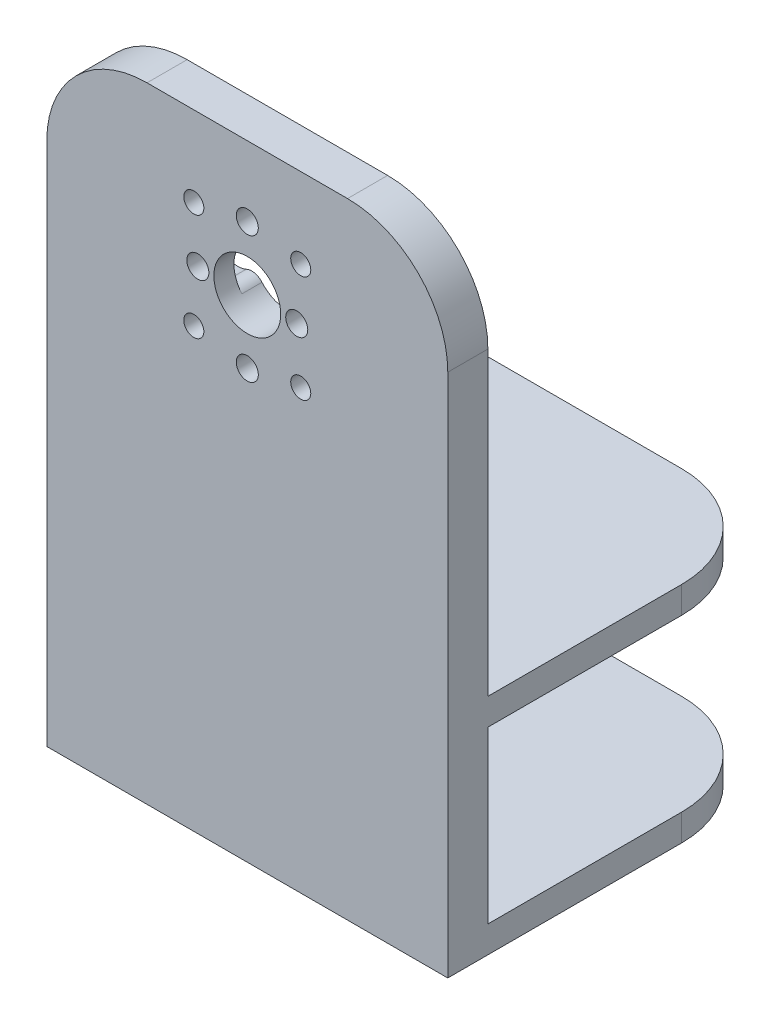
SolidWorks part; units mm, degrees
ref_plane "Front Plane" through (0, 0, 0) normal (0, 0, 1) x (1, 0, 0)
ref_plane "Top Plane" through (0, 0, 0) normal (0, 1, 0) x (1, 0, 0)
ref_plane "Right Plane" through (0, 0, 0) normal (1, 0, 0) x (0, 0, -1)
sketch "Sketch1" plane through (0, 0, 0) normal (0, 0, 1) x (1, 0, 0)
  line L1 (0, 0) -> (60, 0)
  line L2 (0, 0) -> (0, 60)
  line L3 (0, 60) -> (60, 60)
  line L4 (60, 0) -> (60, 60)
  circle A0 centre (30, 40) radius 5
  circle A1 centre (30, 49.5) radius 1.65
  circle A2 centre (30, 30.5) radius 1.65
  circle A3 centre (22.6, 40) radius 1.65
  circle A4 centre (37.4, 40) radius 1.65
  circle A5 centre (22, 48) radius 1.5
  circle A6 centre (38, 48) radius 1.5
  circle A7 centre (38, 32) radius 1.5
  circle A8 centre (22, 32) radius 1.5
  dimension "D3" = 10
  dimension "D10" = 3.3
  dimension "D13" = 3
  dimension "D1" = 60
  dimension "D2" = 60
  dimension "D4" = 30
  dimension "D5" = 20
  dimension "D6" = 19
  dimension "D7" = 9.5
  dimension "D8" = 14.8
  dimension "D9" = 7.4
  dimension "D11" = 8
  dimension "D12" = 8
  dimension "D14" = 4
extrude "Boss-Extrude1" add sketch "Sketch1" along normal blind 6
sketch "Sketch2" plane through (60, 0, 0) normal (1, 0, 0) x (0, 0, -1)
  line L0 (0, 0) -> (0, 60) construction
  line L1 (-6, 0) -> (44, 0)
  line L2 (-6, 0) -> (-6, -4)
  line L3 (-6, -4) -> (44, -4)
  line L4 (44, 0) -> (44, -4)
  line L5 (-6, -4) -> (0, -4)
  line L6 (-6, -4) -> (-6, -29.5)
  line L7 (-6, -29.5) -> (0, -29.5)
  line L8 (0, -4) -> (0, -29.5)
  line L9 (-6, -29.5) -> (44, -29.5)
  line L10 (-6, -29.5) -> (-6, -33.5)
  line L11 (-6, -33.5) -> (44, -33.5)
  line L12 (44, -29.5) -> (44, -33.5)
  dimension "D1" = 4
  dimension "D2" = 50
  dimension "D3" = 4
  dimension "D4" = 50
  dimension "D5" = 25.5
extrude "Boss-Extrude2" add sketch "Sketch2" against normal blind 60 contours L2 L1 L4 L3 | L6 L5 L8 L7 | L10 L9 L12 L11
fillet "Fillet1" radius 15 6 edges at (60, -31.5, -44) (0, -31.5, -44) (60, -2, -44) (0, -2, -44) (0, 60, 3) (60, 60, 3)
sketch "Sketch3" plane through (0, 0, 0) normal (0, 0, -1) x (-1, 0, 0)
  circle A0 centre (-30, 49.5) radius 3
  circle A1 centre (-22.6, 40) radius 3
  circle A2 centre (-30, 30.5) radius 3
  circle A3 centre (-37.4, 40) radius 3
  dimension "D1" = 6
extrude "Cut-Extrude1" cut sketch "Sketch3" against normal blind 3
fillet "Fillet2" radius 2 4 edges at (25.2189, 41.4633, 1.5) (25.2189, 38.5367, 1.5) (34.7811, 38.5367, 1.5) (34.7811, 41.4633, 1.5)
